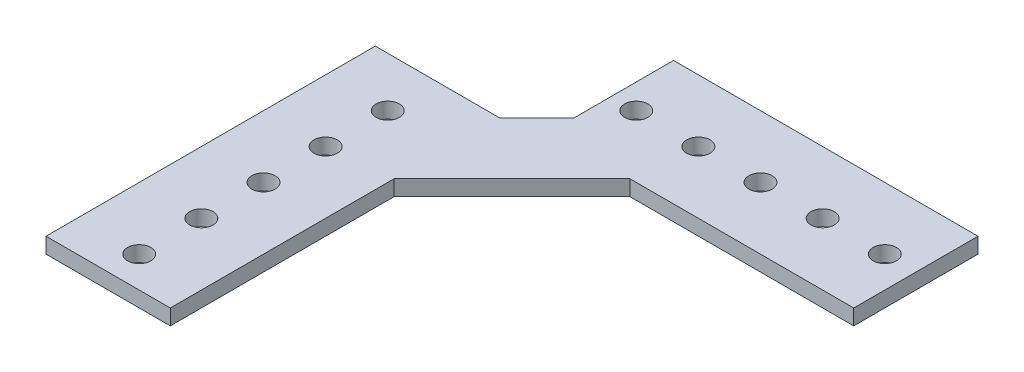
SolidWorks part; units mm, degrees
ref_plane "Front Plane" through (0, 0, 0) normal (0, 0, 1) x (1, 0, 0)
ref_plane "Top Plane" through (0, 0, 0) normal (0, 1, 0) x (1, 0, 0)
ref_plane "Right Plane" through (0, 0, 0) normal (1, 0, 0) x (0, 0, -1)
sketch "Sketch1" plane through (0, 0, 0) normal (0, 1, 0) x (1, 0, 0)
  line L2 (0, 12.7) -> (0, 67.31)
  line L4 (25.4, 12.7) -> (25.4, 45.7574)
  line L5 (33.02, 95.25) -> (95.25, 95.25)
  line L13 (0, 67.31) -> (25.4, 67.31)
  line L14 (0, 67.31) -> (0, 12.7)
  line L16 (25.4, 45.7574) -> (25.4, 12.7)
  line L17 (33.02, 95.25) -> (95.25, 95.25)
  line L18 (33.02, 95.25) -> (33.02, 74.93)
  line L19 (49.4926, 69.85) -> (95.25, 69.85)
  line L20 (95.25, 95.25) -> (95.25, 69.85)
  line L23 (49.4926, 69.85) -> (95.25, 69.85)
  line L24 (25.4, 67.31) -> (33.02, 74.93)
  line L25 (25.4, 45.7574) -> (49.4926, 69.85)
  line L27 (0, 12.7) -> (25.4, 12.7)
  line L28 (0, 12.7) -> (0, 0)
  line L29 (0, 0) -> (25.4, 0)
  line L30 (25.4, 12.7) -> (25.4, 0)
  circle A2 centre (38.1, 82.55) radius 2.3812
  circle A3 centre (50.8, 82.55) radius 2.3812
  circle A4 centre (63.5, 82.55) radius 2.3813
  circle A5 centre (12.7, 57.15) radius 2.3812
  circle A6 centre (12.7, 44.45) radius 2.3812
  circle A7 centre (12.7, 31.75) radius 2.3813
  circle A8 centre (12.7, 19.05) radius 2.3813
  circle A9 centre (76.2, 82.55) radius 2.3813
  circle A10 centre (88.9, 82.55) radius 2.3813
  circle A11 centre (12.7, 6.35) radius 2.3813
  point P3 (12.7, 67.31)
  point P5 (95.25, 82.55)
  point P7 (0, 0)
  point P8 (-0.0697, 12.8623)
  point P9 (0, 0)
  point P10 (0, 0)
  dimension "D5" = 7.62
  dimension "D21" = 15.24
  dimension "D22" = 12.7
  dimension "D17" = 4.7625
  dimension "D3" = 25.4
  dimension "D4" = 33.0574
  dimension "D6" = 24.0926
  dimension "D7" = 45.7574
  dimension "D8" = 12.7
  dimension "D9" = 12.7
  dimension "D10" = 25.4
  dimension "D11" = 12.7
  dimension "D12" = 12.7
  dimension "D13" = 12.7
  dimension "D14" = 6.35
  dimension "D15" = 12.7
  dimension "D16" = 12.7
  dimension "D18" = 12.7
  dimension "D19" = 10.16
  dimension "D20" = 6.35
extrude "Boss-Extrude1" add sketch "Sketch1" along normal blind 3.175
